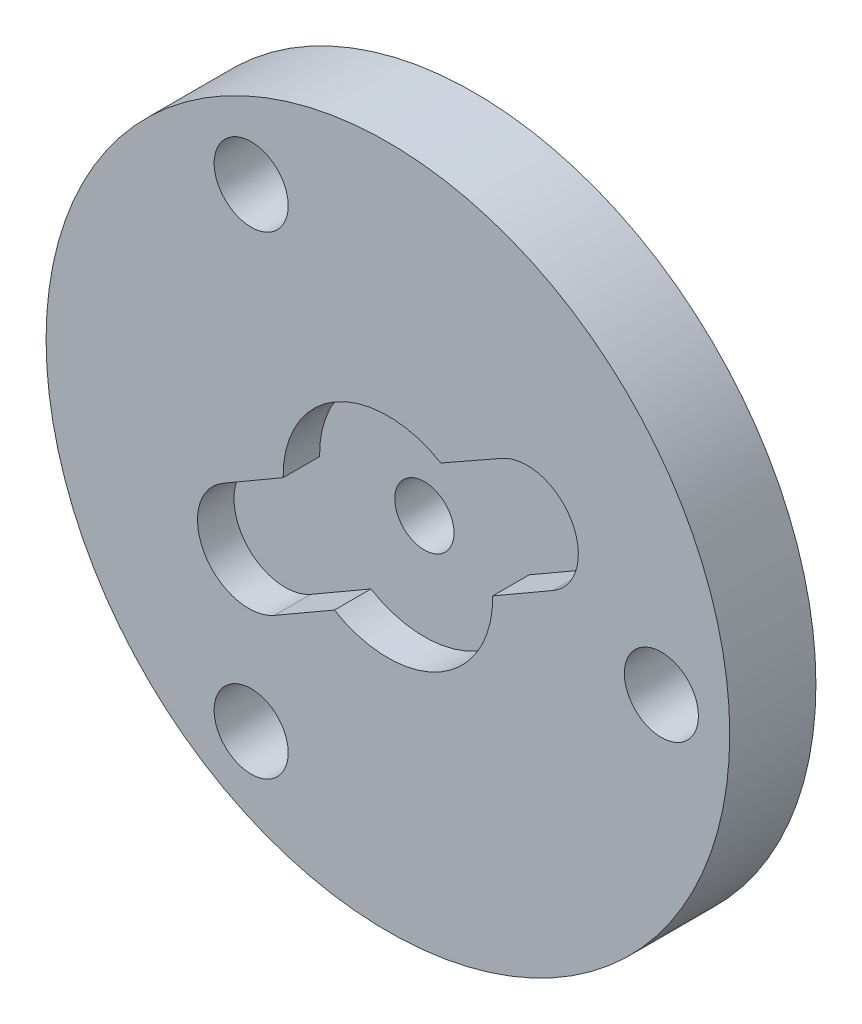
SolidWorks part; units mm, degrees
ref_plane "Piano frontale" through (0, 0, 0) normal (0, 0, 1) x (1, 0, 0)
ref_plane "Piano superiore" through (0, 0, 0) normal (0, 1, 0) x (1, 0, 0)
ref_plane "Piano destro" through (0, 0, 0) normal (1, 0, 0) x (0, 0, -1)
sketch "Schizzo1" plane through (0, 0, 0) normal (0, 0, 1) x (1, 0, 0)
  circle A0 centre (0, 0) radius 15
  dimension "D1" = 30
extrude "Estrusione-Estrusione1" add sketch "Schizzo1" along normal blind 3.7811
sketch "Schizzo2" plane through (0, 0, 3.7811) normal (0, 0, 1) x (1, 0, 0)
  line L0 (12, 0) -> (0, 0)
  line L1 (0, 0) -> (-6.4084, 11.0997)
  line L2 (0, 0) -> (-6.3522, -11.0024)
  circle A0 centre (12, 0) radius 1.625
  circle A1 centre (-6, 10.3923) radius 1.625
  circle A2 centre (-6, -10.3923) radius 1.625
  circle A3 centre (0, 0) radius 1.3
  dimension "D1" = 3.25
  dimension "D9" = 2.6
  dimension "D2" = 12
  dimension "D3" = 120
  dimension "D4" = 120
  dimension "D6" = 12
  dimension "D8" = 12
extrude "Taglio-Estrusione1" cut sketch "Schizzo2" against normal through all
sketch "Schizzo3" plane through (0, 0, 3.7811) normal (0, 0, 1) x (1, 0, 0)
  line L0 (-1.133, 1.9625) -> (-6, 10.3923)
  line L1 (8.054, 4.65) -> (11.4619, 6.6175)
  line L3 (4.9966, 5.4828) -> (2.3247, 3.9694)
  line L4 (2.3247, 3.9694) -> (-7.2349, -1.579)
  line L5 (-4.9805, -5.4736) -> (7.2305, 1.5764)
  line L6 (-8.054, -4.65) -> (-11.1095, -6.4141)
  arc A0 (2.3247, 3.9694) -> (-4.5997, -0.0496) centre (0, 0) ccw
  arc A1 (7.2305, 1.5764) -> (4.9966, 5.4828) centre (6.1055, 3.525) ccw
  arc A3 (-7.2349, -1.579) -> (-4.9805, -5.4736) centre (-6.1055, -3.525) ccw
  arc A4 (-2.3496, -3.9546) -> (4.5996, 0.0575) centre (0, 0) ccw
  circle M5 centre (0, 0) radius 1.3
  dimension "D1" = 9.2
  dimension "D2" = 4.5
  dimension "D4" = 4.5
  dimension "D3" = 7.05
  dimension "D5" = 7.05
extrude "Taglio-Estrusione2" cut sketch "Schizzo3" against normal blind 1.6 contours L4 A3 L5 A1 L3 M5 | L4 A0 L0 | L0 A0 L4 | L5 A4
